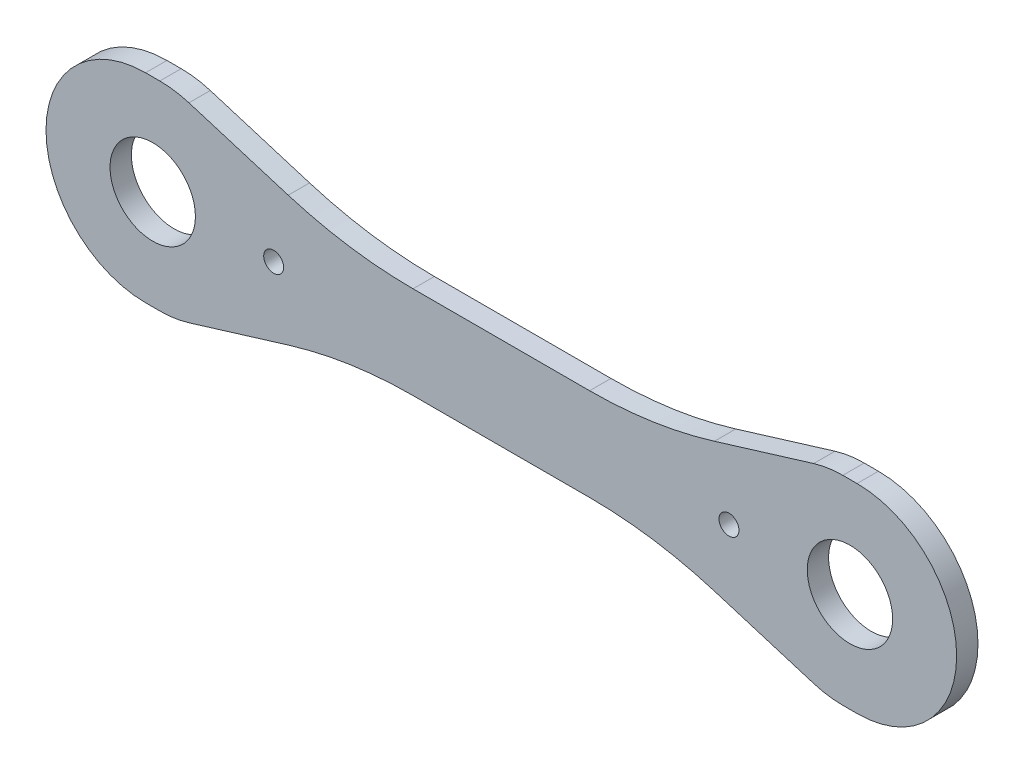
SolidWorks part; units mm, degrees
ref_plane "Plane1" through (0, 0, 0) normal (0, 0, 1) x (1, 0, 0)
ref_plane "Plane2" through (0, 0, 0) normal (0, 1, 0) x (1, 0, 0)
ref_plane "Plane3" through (0, 0, 0) normal (1, 0, 0) x (0, 0, -1)
other "Center of Mass"
sketch "Sketch1" plane through (0, 0, 0) normal (0, 0, 1) x (1, 0, 0)
  line L0 (0, 0) -> (0, 32.5) construction
  line L1 (0, 0) -> (-245, 0) construction
  line L2 (-250, 70) -> (-240, 70)
  line L3 (-219.534, 66.9413) -> (-149.7577, 45.6086)
  line L4 (-62.0462, 32.5) -> (62.0462, 32.5)
  line L5 (-62.0462, -32.5) -> (62.0462, -32.5)
  line L6 (-219.534, -66.9413) -> (-149.7577, -45.6086)
  line L7 (-250, -70) -> (-240, -70)
  line L8 (250, -70) -> (240, -70)
  line L9 (219.534, -66.9413) -> (149.7577, -45.6086)
  line L10 (219.534, 66.9413) -> (149.7577, 45.6086)
  line L11 (250, 70) -> (240, 70)
  circle A0 centre (-245, 0) radius 30 construction
  arc A1 (-250, 70) -> (-250, -70) centre (-250, 0) ccw
  arc A2 (-240, 70) -> (-219.534, 66.9413) centre (-240, 0) cw
  arc A3 (-149.7577, 45.6086) -> (-62.0462, 32.5) centre (-62.0462, 332.5) ccw
  arc A4 (-149.7577, -45.6086) -> (-62.0462, -32.5) centre (-62.0462, -332.5) cw
  arc A5 (-240, -70) -> (-219.534, -66.9413) centre (-240, 0) ccw
  arc A6 (240, -70) -> (219.534, -66.9413) centre (240, 0) cw
  arc A7 (149.7577, -45.6086) -> (62.0462, -32.5) centre (62.0462, -332.5) ccw
  arc A8 (149.7577, 45.6086) -> (62.0462, 32.5) centre (62.0462, 332.5) cw
  arc A9 (240, 70) -> (219.534, 66.9413) centre (240, 0) ccw
  arc A10 (250, 70) -> (250, -70) centre (250, 0) cw
  circle A11 centre (245, 0) radius 30 construction
  circle A12 centre (-160, 0) radius 7 construction
  circle A13 centre (160, 0) radius 7 construction
  dimension "D1" = 60
  dimension "D4" = 70
  dimension "D7" = 300
  dimension "D10" = 14
  dimension "D2" = 5
  dimension "D3" = 5
  dimension "D5" = 65
  dimension "D6" = 17
  dimension "D8" = 490
  dimension "D9" = 85
extrude "Extrude1" add sketch "Sketch1" along normal blind 15
cosmetic thread "Cosmetic Thread1" parameters "D2"=16
sketch "Sketch2" plane through (0, 0, 15) normal (0, 0, 1) x (1, 0, 0)
  circle A0 centre (245, 0) radius 30 construction
  circle A1 centre (-245, 0) radius 30 construction
  circle A2 centre (245, 0) radius 30
  circle A3 centre (-245, 0) radius 30
extrude "ø60 udboringer" cut sketch "Sketch2" against normal through all
sketch "Sketch3" plane through (0, 0, 15) normal (0, 0, 1) x (1, 0, 0)
  circle A0 centre (160, 0) radius 7 construction
  circle A1 centre (-160, 0) radius 7 construction
  circle A2 centre (160, 0) radius 7
  circle A3 centre (-160, 0) radius 7
extrude "M16 gevindhuller" cut sketch "Sketch3" against normal through all
cosmetic thread "Cosmetic Thread2" parameters "D2"=16
cosmetic thread "Cosmetic Thread3" parameters "D2"=16
ref_plane "Plane4" through (0, 0, 7.5) normal (0, 0, -1) x (-1, 0, 0)
sketch "Sketch4" plane through (0, 0, 7.5) normal (0, 0, -1) x (-1, 0, 0)
  circle A0 centre (-245, 0) radius 30 construction
  circle A1 centre (-245, 0) radius 30
